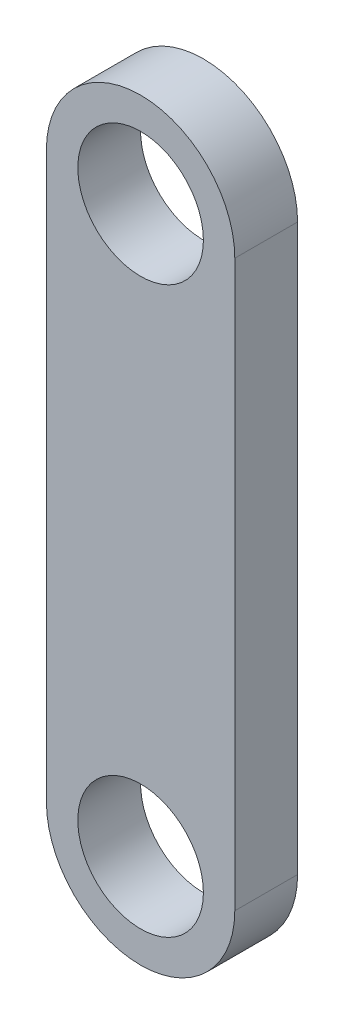
SolidWorks part; units mm, degrees
ref_plane "Front Plane" through (0, 0, 0) normal (0, 0, 1) x (1, 0, 0)
ref_plane "Top Plane" through (0, 0, 0) normal (0, 1, 0) x (1, 0, 0)
ref_plane "Right Plane" through (0, 0, 0) normal (1, 0, 0) x (0, 0, -1)
sketch "Sketch1" plane through (0, 0, 0) normal (0, 0, 1) x (1, 0, 0)
  line L0 (64.9971, 56.5048) -> (64.9971, 11.5048) construction
  line L1 (72.4971, 56.5048) -> (72.4971, 11.5048)
  line L2 (57.4971, 56.5048) -> (57.4971, 11.5048)
  arc A0 (72.4971, 56.5048) -> (57.4971, 56.5048) centre (64.9971, 56.5048) ccw
  arc A1 (57.4971, 11.5048) -> (72.4971, 11.5048) centre (64.9971, 11.5048) ccw
  circle A2 centre (64.9971, 56.5048) radius 5
  circle A3 centre (64.9971, 11.5048) radius 5
  point P2 (64.9971, 34.0048)
  dimension "D2" = 10
  dimension "D1" = 45
  dimension "D3" = 15
extrude "Boss-Extrude1" add sketch "Sketch1" along normal mid plane 5
scale "Scale1" bodies to scale 101 scale about centroid uniform scaling yes scale factor 0.3
